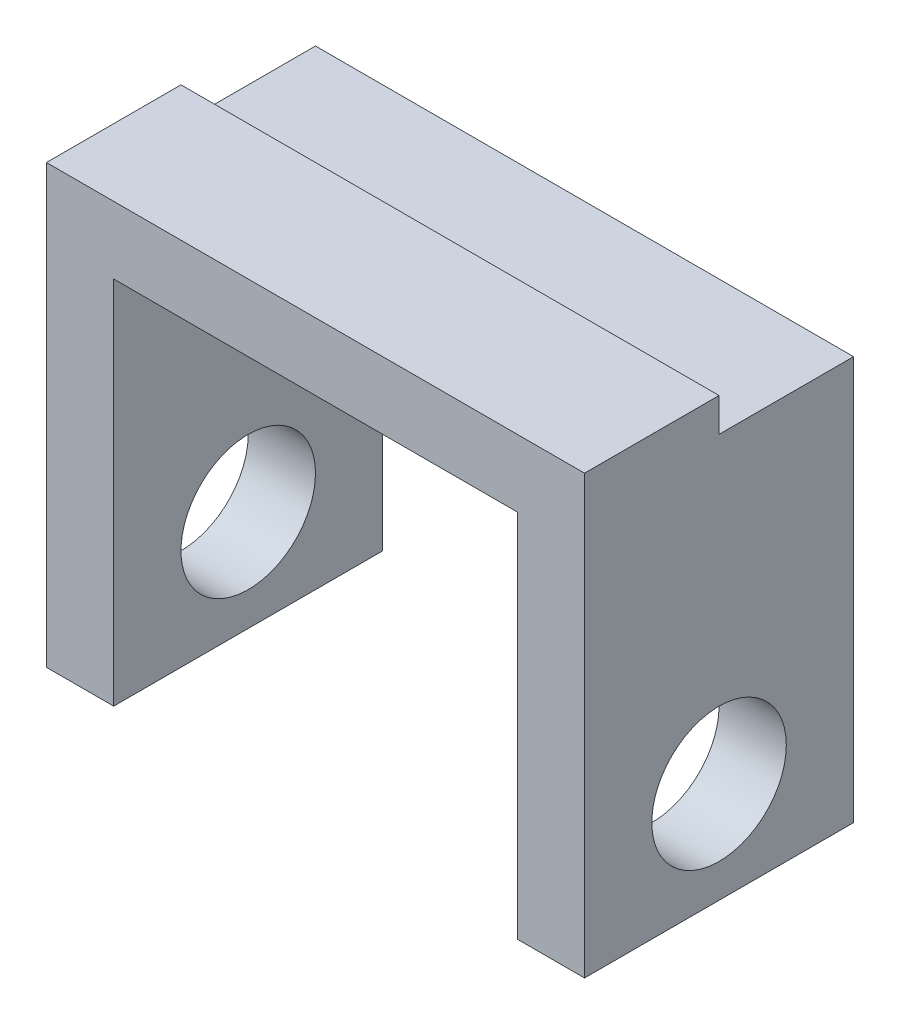
SolidWorks part; units mm, degrees
ref_plane "Alzado" through (0, 0, 0) normal (0, 0, 1) x (1, 0, 0)
ref_plane "Planta" through (0, 0, 0) normal (0, 1, 0) x (1, 0, 0)
ref_plane "Vista lateral" through (0, 0, 0) normal (1, 0, 0) x (0, 0, -1)
sketch "Croquis1" plane through (0, 0, 0) normal (1, 0, 0) x (0, 0, -1)
  line L1 (-20, 50) -> (20, 50)
  line L2 (-20, 50) -> (-20, -15)
  line L3 (-20, -15) -> (20, -15)
  line L4 (20, 50) -> (20, -15)
  circle A0 centre (0, 0) radius 10
  point P7 (0, -15)
  dimension "D1" = 20
  dimension "D2" = 40
  dimension "D3" = 50
  dimension "D4" = 15
extrude "Saliente-Extruir1" add sketch "Croquis1" along normal mid plane 80
sketch "Croquis2" plane through (0, 0, 0) normal (0, 0, 1) x (1, 0, 0)
  line L0 (40, -15) -> (-40, -15) construction
  line L1 (-30, -15) -> (30, -15)
  line L2 (-30, -15) -> (-30, 40)
  line L3 (-30, 40) -> (30, 40)
  line L4 (30, -15) -> (30, 40)
  line L5 (40, 50) -> (-40, 50) construction
  point P6 (0, -15)
  dimension "D1" = 60
  dimension "D2" = 10
extrude "Cortar-Extruir1" cut sketch "Croquis2" against normal through all both and the other way through all contours L3 L4 L1 L2
sketch "Croquis3" plane through (0, 0, 0) normal (1, 0, 0) x (0, 0, -1)
  line L0 (0, 0) -> (0, 50) construction
  line L1 (20, 50) -> (-20, 50) construction
  line L2 (20, -15) -> (20, 50) construction
  line L3 (0, 50) -> (20, 50)
  line L4 (0, 50) -> (0, 45)
  line L5 (0, 45) -> (20, 45)
  line L6 (20, 50) -> (20, 45)
  dimension "D1" = 5
extrude "Cortar-Extruir2" cut sketch "Croquis3" against normal through all both and the other way through all
